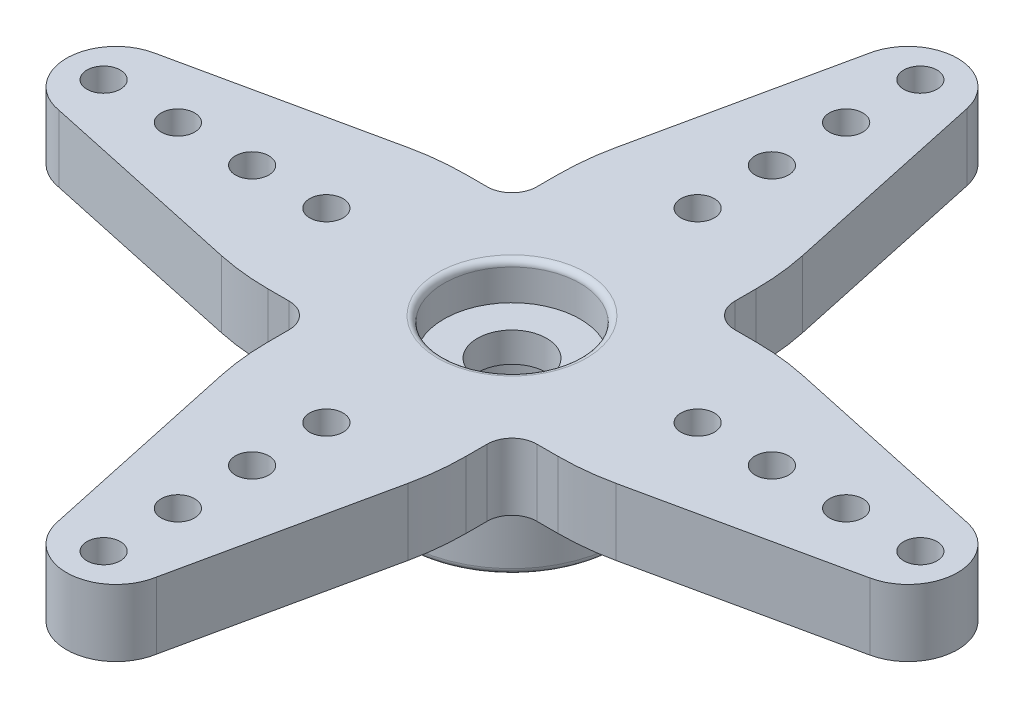
SolidWorks part; units mm, degrees
ref_plane "Plan de face" through (0, 0, 0) normal (0, 0, 1) x (1, 0, 0)
ref_plane "Plan de dessus" through (0, 0, 0) normal (0, 1, 0) x (1, 0, 0)
ref_plane "Plan de droite" through (0, 0, 0) normal (1, 0, 0) x (0, 0, -1)
sketch "Esquisse1" plane through (0, 0, 0) normal (0, 1, 0) x (1, 0, 0)
  line L0 (0, 18.4549) -> (0, -10.284) construction
  line L1 (-4, 5.8623) -> (-4, 5)
  line L3 (1.9552, 16.4212) -> (3.7758, 7.9691)
  line L4 (-1.9723, 16.3318) -> (-3.7753, 7.9702)
  line L14 (5.8623, 4) -> (5, 4)
  line L15 (16.3318, 1.9723) -> (7.9702, 3.7753)
  line L16 (16.4212, -1.9552) -> (7.9691, -3.7758)
  line L17 (5.8634, -4) -> (5, -4)
  line L18 (4, -5.8623) -> (4, -5)
  line L19 (1.9723, -16.3318) -> (3.7753, -7.9702)
  line L20 (-1.9552, -16.4212) -> (-3.7758, -7.9691)
  line L21 (-4, -5.8634) -> (-4, -5)
  line L22 (-5.8623, -4) -> (-5, -4)
  line L23 (-16.3318, -1.9723) -> (-7.9702, -3.7753)
  line L24 (4, 5.8634) -> (4, 5)
  line L25 (-16.4212, 1.9552) -> (-7.9691, 3.7758)
  line L26 (-5.8634, 4) -> (-5, 4)
  circle A0 centre (0, 0) radius 1.4
  circle A1 centre (0, 0) radius 18 construction
  circle A2 centre (0, 0) radius 8 construction
  arc A3 (1.9552, 16.4212) -> (-1.9723, 16.3318) centre (0, 16) ccw
  circle A4 centre (0, 16.5) radius 0.675
  circle A5 centre (0, 10.5) radius 0.675
  circle A6 centre (0, 7.5) radius 0.675
  circle A27 centre (0, 13.5) radius 0.675
  arc A28 (3.7758, 7.9691) -> (4, 5.8634) centre (-6, 5.8634) cw
  arc A29 (-3.7753, 7.9702) -> (-4, 5.8623) centre (6, 5.8623) ccw
  arc A30 (7.9702, 3.7753) -> (5.8623, 4) centre (5.8623, -6) ccw
  arc A31 (16.4212, -1.9552) -> (16.3318, 1.9723) centre (16, 0) ccw
  arc A32 (7.9691, -3.7758) -> (5.8634, -4) centre (5.8634, 6) cw
  circle A33 centre (16.5, 0) radius 0.675
  circle A34 centre (13.5, 0) radius 0.675
  circle A35 centre (10.5, 0) radius 0.675
  circle A36 centre (7.5, 0) radius 0.675
  arc A37 (3.7753, -7.9702) -> (4, -5.8623) centre (-6, -5.8623) ccw
  arc A38 (-1.9552, -16.4212) -> (1.9723, -16.3318) centre (0, -16) ccw
  arc A39 (-3.7758, -7.9691) -> (-4, -5.8634) centre (6, -5.8634) cw
  circle A40 centre (0, -16.5) radius 0.675
  circle A41 centre (0, -13.5) radius 0.675
  circle A42 centre (0, -10.5) radius 0.675
  circle A43 centre (0, -7.5) radius 0.675
  circle A44 centre (0, 0) radius 6.65 construction
  arc A45 (-7.9702, -3.7753) -> (-5.8623, -4) centre (-5.8623, 6) ccw
  arc A46 (-16.4212, 1.9552) -> (-16.3318, -1.9723) centre (-16, 0) ccw
  arc A47 (-7.9691, 3.7758) -> (-5.8634, 4) centre (-5.8634, -6) cw
  circle A48 centre (-16.5, 0) radius 0.675
  circle A49 centre (-13.5, 0) radius 0.675
  circle A50 centre (-10.5, 0) radius 0.675
  circle A51 centre (-7.5, 0) radius 0.675
  arc A52 (-5, -4) -> (-4, -5) centre (-5, -5) cw
  arc A53 (4, -5) -> (5, -4) centre (5, -5) cw
  arc A54 (5, 4) -> (4, 5) centre (5, 5) cw
  arc A55 (-5, 4) -> (-4, 5) centre (-5, 5) ccw
  point P25 (4, 6.9282)
  point P28 (-4, 6.9282)
  point P89 (0, 0)
  dimension "D1" = 2.8
  dimension "D2" = 36
  dimension "D3" = 16
  dimension "D6" = 4
  dimension "D7" = 1.35
  dimension "D8" = 1.35
  dimension "D9" = 1.35
  dimension "D11" = 13.3
  dimension "D12" = 7.5
  dimension "D14" = 1.35
  dimension "D16" = 10
  dimension "D18" = 1
  dimension "D4" = 8
  dimension "D5" = 4
  dimension "D10" = 16.5
  dimension "D13" = 10.5
  dimension "D15" = 13.5
  dimension "D17" = 4
extrude "Boss.-Extru.1" add sketch "Esquisse1" along normal blind 2.7
sketch "Esquisse2" plane through (0, 2.7, 0) normal (0, 1, 0) x (1, 0, 0)
  circle A0 centre (0, 0) radius 2.75
  dimension "D1" = 5.5
extrude "Enlèv. mat.-Extru.1" cut sketch "Esquisse2" against normal blind 1.5
sketch "Esquisse3" plane through (0, 0, 0) normal (0, -1, 0) x (1, 0, 0)
  circle A0 centre (0, 0) radius 4.4
  circle A1 centre (0, 0) radius 2.75
  dimension "D1" = 8.8
  dimension "D2" = 5.5
extrude "Boss.-Extru.2" add sketch "Esquisse3" along normal blind 3.3
fillet "Congé1" radius 0.25 3 edges at (0, -3.3, -2.75) (0, -3.3, -4.4) (0, 2.7, 2.75)
